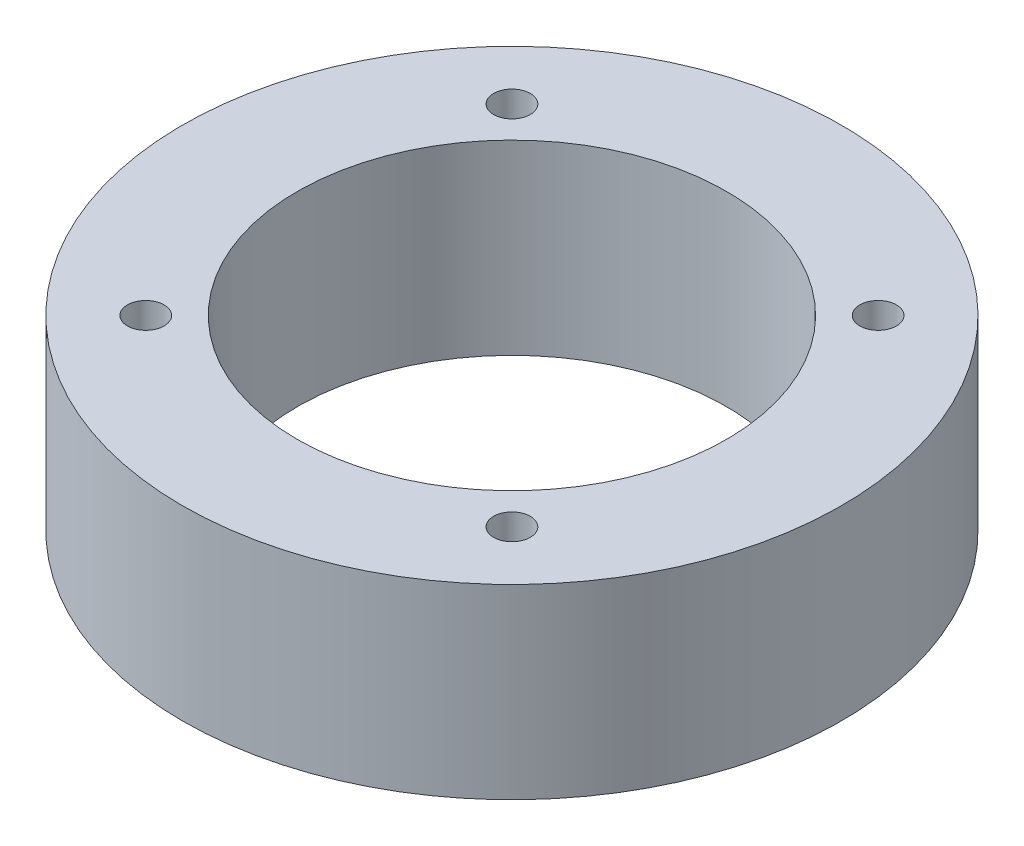
SolidWorks part; units mm, degrees
material "1060 Alloy"
ref_plane "Front Plane" through (0, 0, 0) normal (0, 0, 1) x (1, 0, 0)
ref_plane "Top Plane" through (0, 0, 0) normal (0, 1, 0) x (1, 0, 0)
ref_plane "Right Plane" through (0, 0, 0) normal (1, 0, 0) x (0, 0, -1)
sketch "Sketch1" plane through (0, 0, 0) normal (0, 1, 0) x (1, 0, 0)
  circle A0 centre (0, 0) radius 25.146
  dimension "D1" = 50.292
extrude "Boss-Extrude1" add sketch "Sketch1" along normal blind 14.224
sketch "Sketch2" plane through (0, 14.224, 0) normal (0, 1, 0) x (1, 0, 0)
  line L0 (0, 0) -> (0, 29.6501) construction
  line L1 (0, 0) -> (30.1357, 0) construction
  line L2 (-13.97, -13.97) -> (13.97, -13.97) construction
  line L3 (13.97, -13.97) -> (13.97, 13.97) construction
  line L4 (13.97, 13.97) -> (-13.97, 13.97) construction
  line L5 (-13.97, 13.97) -> (-13.97, -13.97) construction
  circle A0 centre (13.97, 13.97) radius 1.397
  circle A1 centre (13.97, -13.97) radius 1.397
  circle A2 centre (-13.97, -13.97) radius 1.397
  circle A3 centre (-13.97, 13.97) radius 1.397
  dimension "D1" = 27.94
  dimension "D2" = 27.94
  dimension "D3" = 2.794
extrude "Cut-Extrude1" cut sketch "Sketch2" against normal up to next
sketch "Sketch3" plane through (0, 14.224, 0) normal (0, 1, 0) x (1, 0, 0)
  circle A0 centre (0, 0) radius 16.383
  dimension "D1" = 32.766
extrude "Cut-Extrude2" cut sketch "Sketch3" against normal up to next
equation "\"D2@Sketch2\"=\"D1@Sketch2\""
